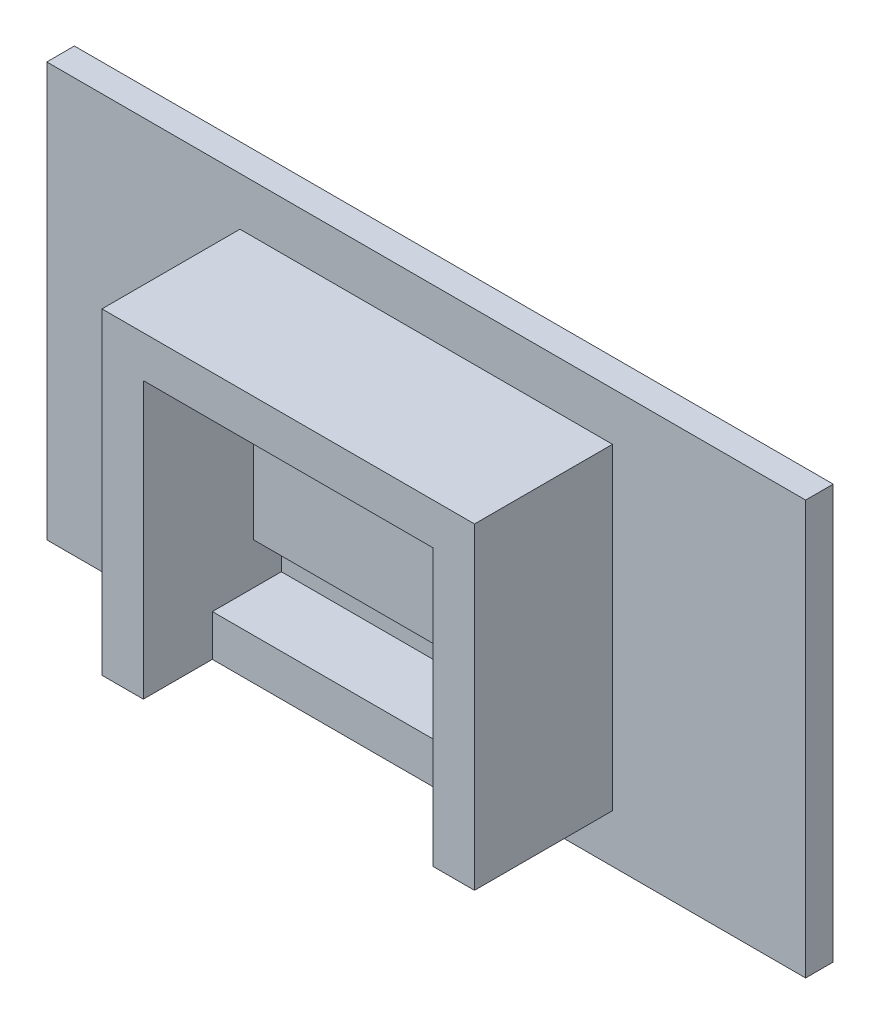
SolidWorks part; units mm, degrees
other "Markup1"
sketch "Sketch7" plane through (27.5, -15, 12) normal (0.1566, -0.6053, 0.7804) x (0.9876, 0.1025, -0.1187)
ref_plane "Front Plane" through (0, 0, 0) normal (0, 0, 1) x (1, 0, 0)
ref_plane "Top Plane" through (0, 0, 0) normal (0, 1, 0) x (1, 0, 0)
ref_plane "Right Plane" through (0, 0, 0) normal (1, 0, 0) x (0, 0, -1)
sketch "Sketch1" plane through (0, 0, 0) normal (0, 0, 1) x (1, 0, 0)
  line L1 (-27.5, -15) -> (27.5, -15)
  line L2 (-27.5, -15) -> (-27.5, 15)
  line L3 (-27.5, 15) -> (27.5, 15)
  line L4 (27.5, -15) -> (27.5, 15)
  line L5 (-27.5, -15) -> (27.5, 15) construction
  line L6 (-27.5, 15) -> (27.5, -15) construction
  point P0 (0, 0)
  dimension "D1" = 30
  dimension "D2" = 55
extrude "Boss-Extrude2" add sketch "Sketch1" along normal blind 2
sketch "Sketch8" plane through (0, 0, 2) normal (0, 0, 1) x (1, 0, 0)
  line L1 (-10.5, 8.5) -> (10.5, 8.5)
  line L2 (-10.5, 8.5) -> (-10.5, -8.5)
  line L3 (-10.5, -8.5) -> (10.5, -8.5)
  line L4 (10.5, 8.5) -> (10.5, -8.5)
  line L5 (-13.5, -11.5) -> (13.5, -11.5)
  line L6 (-13.5, -11.5) -> (-13.5, 11.5)
  line L7 (-13.5, 11.5) -> (13.5, 11.5)
  line L8 (13.5, -11.5) -> (13.5, 11.5)
  line L9 (-13.5, -11.5) -> (13.5, 11.5) construction
  line L10 (-13.5, 11.5) -> (13.5, -11.5) construction
  point P5 (0, 0)
  dimension "D1" = 17
  dimension "D2" = 21
  dimension "D3" = 8.5
  dimension "D4" = 10.5
  dimension "D5" = 27
  dimension "D6" = 11.5
extrude "Boss-Extrude3" add sketch "Sketch8" along normal blind 10
sketch "Sketch10" plane through (0, 0, 2) normal (0, 0, 1) x (1, 0, 0)
  line L0 (10.5, -8.5) -> (10.5, 8.5) construction
  line L1 (-10.5, 8.5) -> (10.5, 8.5)
  line L2 (-10.5, 8.5) -> (-10.5, -5.5)
  line L3 (-10.5, -5.5) -> (10.5, -5.5)
  line L4 (10.5, 8.5) -> (10.5, -5.5)
  dimension "D1" = 14
extrude "Boss-Extrude4" add sketch "Sketch10" along normal blind 2
sketch "Sketch11" plane through (0, 0, 4) normal (0, 0, 1) x (1, 0, 0)
sketch "Sketch13" plane through (0, -11.5, 0) normal (0, -1, 0) x (1, 0, 0)
  line L0 (-13.5, 12) -> (13.5, 12) construction
  line L1 (-10.5, 12) -> (10.5, 12)
  line L2 (-10.5, 12) -> (-10.5, 7)
  line L3 (-10.5, 7) -> (10.5, 7)
  line L4 (10.5, 12) -> (10.5, 7)
  line L5 (-13.5, 12) -> (-13.5, 2) construction
  line L6 (13.5, 12) -> (13.5, 2) construction
  dimension "D1" = 3
  dimension "D2" = 3
  dimension "D3" = 5
extrude "Cut-Extrude3" cut sketch "Sketch13" against normal blind 3
sketch "Sketch14" plane through (0, 0, 4) normal (0, 0, 1) x (1, 0, 0)
  line L0 (-10.5, 8.5) -> (-10.5, -5.5) construction
  line L1 (10.5, 8.5) -> (-10.5, 8.5) construction
  line L2 (10.5, 8.5) -> (-10.5, 8.5) construction
  circle A0 centre (-8, 6) radius 1.5
  circle A1 centre (8, 6) radius 1.5
  dimension "D1" = 3
  dimension "D2" = 3
  dimension "D3" = 16
  dimension "D4" = 2.5
  dimension "D5" = 2.5
  dimension "D6" = 2.5
extrude "Boss-Extrude5" add sketch "Sketch14" along normal blind 3
